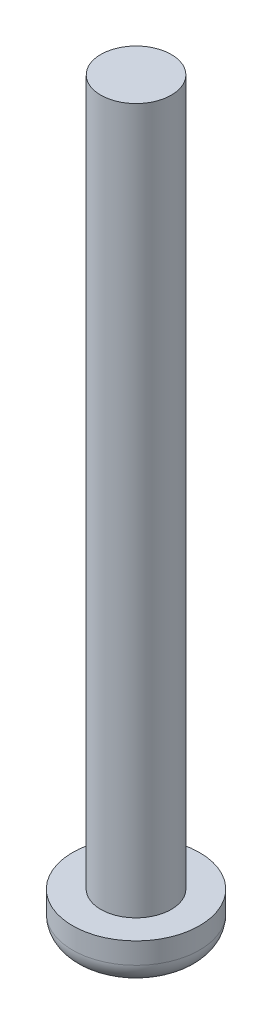
SolidWorks part; units mm, degrees
ref_plane "Front Plane" through (0, 0, 0) normal (0, 0, 1) x (1, 0, 0)
ref_plane "Top Plane" through (0, 0, 0) normal (0, 1, 0) x (1, 0, 0)
ref_plane "Right Plane" through (0, 0, 0) normal (1, 0, 0) x (0, 0, -1)
sketch "Sketch1" plane through (0, 0, 0) normal (0, 1, 0) x (1, 0, 0)
  circle A0 centre (0, 0) radius 0.5
  dimension "D1" = 1
extrude "Boss-Extrude1" add sketch "Sketch1" along normal blind 10
sketch "Sketch2" plane through (0, 0, 0) normal (0, -1, 0) x (1, 0, 0)
  circle A0 centre (0, 0) radius 0.9
  dimension "D1" = 1.8
extrude "Boss-Extrude2" add sketch "Sketch2" along normal blind 0.6
fillet "Fillet1" radius 0.3 1 edges at (0, -0.6, -0.9)
